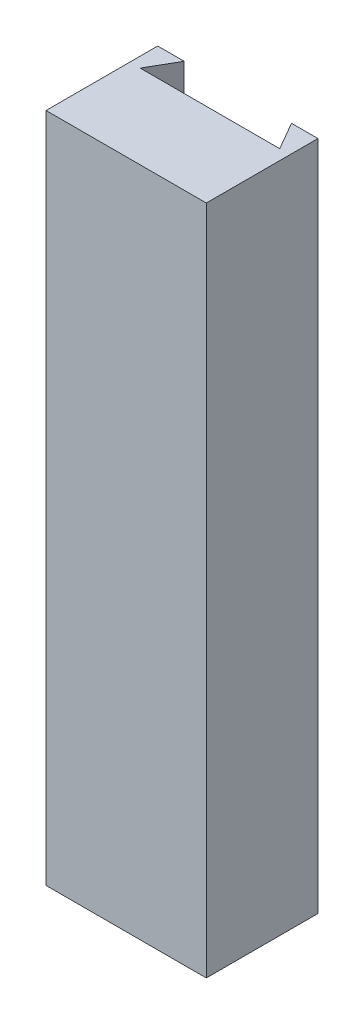
SolidWorks part; units mm, degrees
ref_plane "Ebene vorne" through (0, 0, 0) normal (0, 0, 1) x (1, 0, 0)
ref_plane "Ebene oben" through (0, 0, 0) normal (0, 1, 0) x (1, 0, 0)
ref_plane "Ebene rechts" through (0, 0, 0) normal (1, 0, 0) x (0, 0, -1)
sketch "Sketch1" plane through (0, 0, 0) normal (0, 0, 1) x (1, 0, 0)
  line L1 (-1.435, 0) -> (1.435, 0)
  line L2 (-1.435, 0) -> (-1.435, 12.02)
  line L3 (-1.435, 12.02) -> (1.435, 12.02)
  line L4 (1.435, 0) -> (1.435, 12.02)
  line L5 (-1.435, 0) -> (1.435, 12.02) construction
  line L6 (-1.435, 12.02) -> (1.435, 0) construction
  point P0 (0, 6.01)
  point P5 (0, 0)
  dimension "D1" = 0
  dimension "D2" = 2.87
  dimension "D3" = 12.02
extrude "Boss-Extrude1" add sketch "Sketch1" along normal blind 2
sketch "Sketch2" plane through (0, 0, 0) normal (0, -1, 0) x (1, 0, 0)
  line L0 (-1.435, 0) -> (1.435, 0) construction
  line L1 (0, -1.6651) -> (1.25, 0.5)
  line L2 (1.25, 0.5) -> (-1.25, 0.5)
  line L3 (-1.25, 0.5) -> (0, -1.6651)
  circle A0 centre (0, -0.2217) radius 0.7217 construction
  point P1 (-0.4574, -1.3351)
  point P8 (0, -0.1579)
  dimension "D1" = 2.5
  dimension "D2" = 0
  dimension "D3" = 0.5
extrude "Cut-Extrude1" cut sketch "Sketch2" against normal up to next
